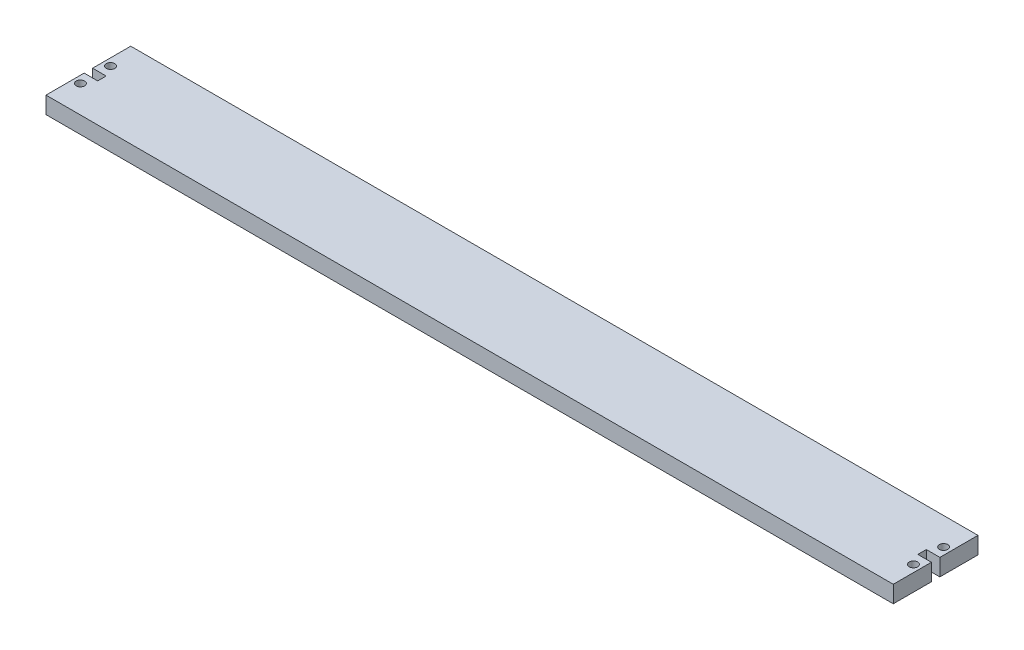
SolidWorks part; units mm, degrees
ref_plane "Front Plane" through (0, 0, 0) normal (0, 0, 1) x (1, 0, 0)
ref_plane "Top Plane" through (0, 0, 0) normal (0, 1, 0) x (1, 0, 0)
ref_plane "Right Plane" through (0, 0, 0) normal (1, 0, 0) x (0, 0, -1)
sketch "Sketch1" plane through (0, 0, 0) normal (0, 1, 0) x (1, 0, 0)
  line L1 (0, 0) -> (500, 0)
  line L2 (0, 0) -> (0, -50)
  line L3 (0, -50) -> (500, -50)
  line L4 (500, 0) -> (500, -50)
extrude "Boss-Extrude1" add sketch "Sketch1" along normal blind 10
sketch "Sketch2" plane through (0, 10, 0) normal (0, 1, 0) x (1, 0, 0)
  line L0 (0, -50) -> (4.2, -50) construction
  line L1 (0, -50) -> (500, -50) construction
  line L2 (4.2, -50) -> (4.2, -25) construction
  line L3 (4.2, -25) -> (4.2, 0) construction
  line L4 (500, 0) -> (0, 0) construction
  line L5 (4.2, -25) -> (4.2, -16.1) construction
  line L6 (0, -25) -> (0, -22.5)
  line L8 (0, 0) -> (0, -50) construction
  line L9 (0, -22.5) -> (8, -22.5)
  line L10 (8, -22.5) -> (8, -27.5)
  line L11 (8, -27.5) -> (0, -27.5)
  line L12 (0, -27.5) -> (0, -25)
  line L13 (250, 0) -> (250, -50) construction
  line L14 (495.8, -25) -> (495.8, -16.1) construction
  line L15 (495.8, -25) -> (495.8, 0) construction
  line L16 (495.8, -50) -> (495.8, -25) construction
  line L17 (500, -50) -> (495.8, -50) construction
  line L18 (500, -27.5) -> (500, -25)
  line L19 (492, -27.5) -> (500, -27.5)
  line L20 (492, -22.5) -> (492, -27.5)
  line L21 (500, -22.5) -> (492, -22.5)
  line L22 (500, -25) -> (500, -22.5)
  circle A0 centre (4.2, -16.1) radius 2.5
  circle A1 centre (4.2, -33.9) radius 2.5
  circle A2 centre (495.8, -33.9) radius 2.5
  circle A3 centre (495.8, -16.1) radius 2.5
extrude "Cut-Extrude1" cut sketch "Sketch2" against normal blind 10
